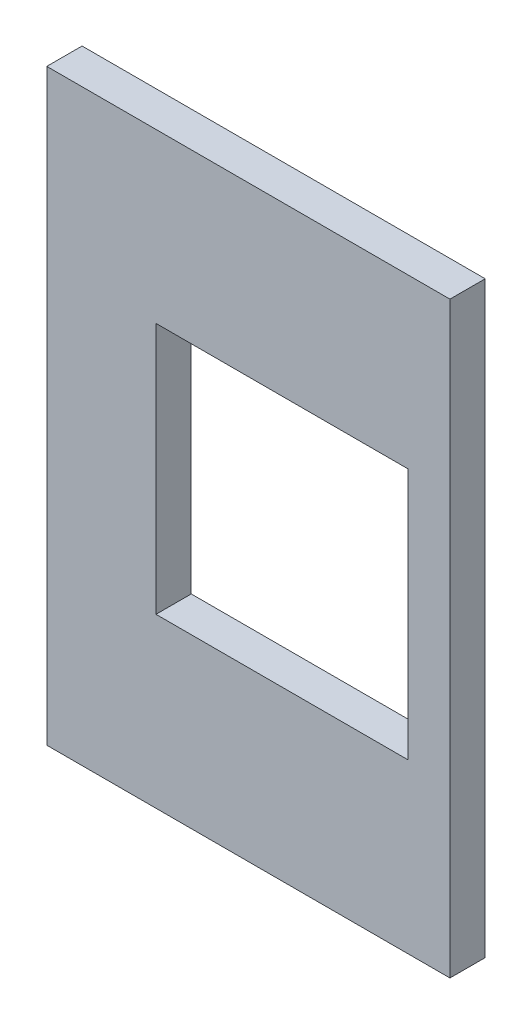
SolidWorks part; units mm, degrees
ref_plane "Front Plane" through (0, 0, 0) normal (0, 0, 1) x (1, 0, 0)
ref_plane "Top Plane" through (0, 0, 0) normal (0, 1, 0) x (1, 0, 0)
ref_plane "Right Plane" through (0, 0, 0) normal (1, 0, 0) x (0, 0, -1)
sketch "Sketch1" plane through (0, 0, 0) normal (0, 0, 1) x (1, 0, 0)
  line L0 (0, 22.225) -> (0, -22.225) construction
  line L1 (-12.7, -22.225) -> (12.7, -22.225)
  line L2 (-12.7, -22.225) -> (-12.7, 22.225)
  line L3 (-12.7, 22.225) -> (12.7, 22.225)
  line L4 (12.7, -22.225) -> (12.7, 22.225)
  line L5 (-12.7, -22.225) -> (12.7, 22.225) construction
  line L6 (-12.7, 22.225) -> (12.7, -22.225) construction
  line L7 (-9.525, 9.525) -> (9.525, 9.525)
  line L8 (-9.525, 9.525) -> (-9.525, -9.525)
  line L9 (-9.525, -9.525) -> (9.525, -9.525)
  line L10 (9.525, 9.525) -> (9.525, -9.525)
  point P0 (0, 0)
  dimension "D1" = 25.4
  dimension "D2" = 19.05
  dimension "D3" = 19.05
  dimension "D4" = 12.7
  dimension "D5" = 12.7
extrude "Boss-Extrude1" add sketch "Sketch1" along normal blind 3.175
ref_plane "Plane1" through (6.35, 0, 0) normal (1, 0, 0) x (0, 0, -1)
sketch "Sketch2" plane through (6.35, 0, 0) normal (1, 0, 0) x (0, 0, -1)
  line L0 (0, -9.525) -> (5.715, -9.525)
  line L1 (0, -22.225) -> (0, 22.225) construction
  line L2 (0, -22.225) -> (5.715, -22.225)
  line L3 (0, -9.525) -> (0, -22.225)
  circle A0 centre (5.715, -15.875) radius 3.175
  arc A1 (5.715, -22.225) -> (5.715, -9.525) centre (5.715, -15.875) ccw
  dimension "D1" = 3.175
  dimension "D2" = 6.35
  dimension "D3" = 2.54
extrude "Boss-Extrude2" [suppressed] add sketch "Sketch2" against normal blind 3.175
mirror "Mirror1" [suppressed] about plane through (0, 0, 0) normal (1, 0, 0)
sketch "Sketch3" plane through (0, 0, 0) normal (0, 0, -1) x (-1, 0, 0)
  line L4 (-12.7, -22.225) -> (12.7, -22.225)
  line L5 (-12.7, 22.225) -> (-12.7, -22.225)
  line L6 (-12.7, 22.225) -> (-12.7, -22.225)
  line L7 (12.7, -22.225) -> (12.7, 22.225)
  line L8 (-12.7, -22.225) -> (12.7, -22.225)
  line L12 (12.7, -22.225) -> (12.7, 22.225)
  line L13 (12.7, 22.225) -> (-12.7, 22.225)
  line L14 (12.7, 22.225) -> (-12.7, 22.225)
  dimension "D1" = 0
extrude "Cut-Extrude1" [suppressed] cut sketch "Sketch3" against normal through all
sketch "Sketch4" plane through (-12.7, 0, 0) normal (-1, 0, 0) x (0, 0, 1)
  line L4 (0, 22.225) -> (0, -22.225)
  line L5 (0, -22.225) -> (3.175, -22.225)
  line L6 (3.175, -22.225) -> (3.175, 22.225)
  line L7 (3.175, 22.225) -> (0, 22.225)
  line L8 (0, 22.225) -> (0, -22.225)
  line L9 (0, -22.225) -> (3.175, -22.225)
  line L10 (3.175, -22.225) -> (3.175, 22.225)
  line L11 (3.175, 22.225) -> (0, 22.225)
  dimension "D1" = 0
extrude "Boss-Extrude3" add sketch "Sketch4" along normal blind 5.08
other "Move Face1" face at (-2.54, 0, 3.175) parameters "D1"=0.508
